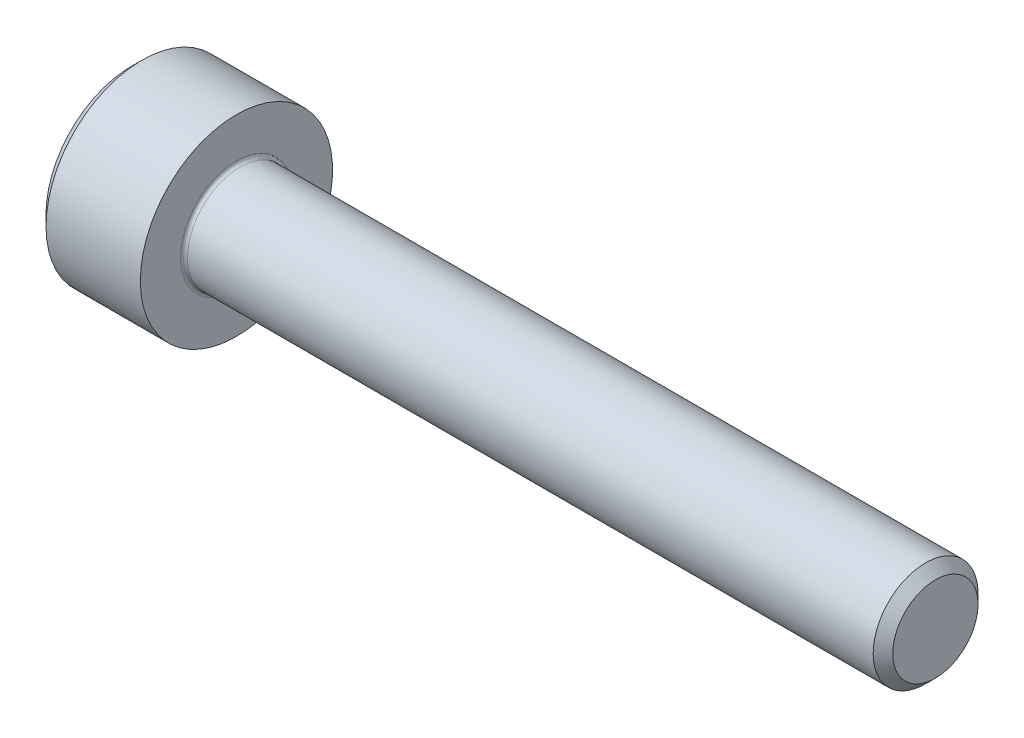
SolidWorks part; units mm, degrees
revolve "Base-Revolve" add sketch "BodySke"
sketch "BodySke" plane through (0, 0, 0) normal (0, 0, 1) x (1, 0, 0)
  line L0 (0, 0) -> (0, 2.45)
  line L1 (0.3, 2.75) -> (3, 2.75)
  line L2 (3, 2.75) -> (3, 1.5)
  line L3 (3, 1.5) -> (22.7195, 1.5)
  line L4 (23, 1.2195) -> (23, 0)
  line L5 (23, 0) -> (0, 0)
  line L6 (-31.75, 0) -> (127, 0) construction
  line L7 (0, 2.45) -> (0.3, 2.75)
  line L8 (23, 1.2195) -> (22.7195, 1.5)
  line L9 (0, -2.45) -> (0.3, -2.75) construction
  line L10 (23, -1.2195) -> (22.7195, -1.5) construction
  line L11 (3.5, 9.525) -> (3.5, 3.175) construction
  line L12 (3, 9.525) -> (3, 3.175) construction
  line L13 (-27, 9.525) -> (-27, 3.175) construction
  dimension "Diameter" = 3
  dimension "Head_ht" = 3
  dimension "Length" = 20
  dimension "Body_ch_ang" = 45
  dimension "Head_dia" = 5.5
  dimension "Head_ch_ang" = 45
  dimension "Minor_dia" = 2.439
  dimension "Advance" = 0.5
  dimension "Thread_nom" = 20
  dimension "Thread_length" = 50
  dimension "Head_ch_ht" = 0.3
cosmetic thread "ThreadCosmetic"
fillet "Fillet1" radius 0.1 1 edges at (3, 0, 1.5)
ref_plane "Plane1" through (0, 0, 0) normal (0, 0, 1) x (1, 0, 0)
ref_plane "Plane2" through (0, 0, 0) normal (0, 1, 0) x (1, 0, 0)
ref_plane "Plane3" through (0, 0, 0) normal (1, 0, 0) x (0, 0, -1)
sketch "Sketch2" plane through (0, 0, 0) normal (0, 0, 1) x (1, 0, 0)
  line L0 (0, 1.28) -> (1.3, 1.28)
  line L1 (1.3, 1.28) -> (2.039, 0)
  line L2 (-31.75, 0) -> (127, 0) construction
  line L3 (2.039, 0) -> (0, 0)
  line L4 (0, 0) -> (0, 1.28)
  line L5 (0, 2.45) -> (0, -2.45) construction
  line L6 (0, 0) -> (47.625, 0) construction
  line L7 (3, -2.75) -> (3, 2.75) construction
  dimension "D1" = 1.28
  dimension "D2" = 60
revolve "Hex-PreBroach" cut sketch "Sketch2" angle 360 about L6
sketch "Sketch3" plane through (0, 0, 0) normal (-1, 0, 0) x (0, 0.5, 0.866)
  line L0 (0.739, 1.28) -> (-0.739, 1.28)
  line L1 (-0.739, 1.28) -> (-1.478, 0)
  line L2 (0.739, 1.28) -> (1.478, 0)
  line L3 (0.739, -1.28) -> (1.478, 0)
  line L4 (0.739, -1.28) -> (-0.739, -1.28)
  line L5 (-0.739, -1.28) -> (-1.478, 0)
  dimension "D1" = 1.28
  dimension "D2" = 1.28
  dimension "Hex_size" = 2.56
extrude "Hex" cut sketch "Sketch3" against normal blind 1.3
sketch "Sketch4" plane through (0, 0, 0) normal (-1, 0, 0) x (0, 0, 1)
  line L0 (0, 0) -> (1.4605, 0)
  line L1 (0, 0) -> (6.1484, 3.5498) construction
  line L2 (0, 0) -> (0.7302, 1.2648)
  line L3 (1.2009, 0.3267) -> (1.3933, 0.4378)
  line L4 (0.8834, 0.8767) -> (1.0758, 0.9877)
  arc A0 (1.2009, 0.3267) -> (0.8834, 0.8767) centre (0, 0) ccw
  arc A1 (1.4605, 0) -> (1.3933, 0.4378) centre (0, 0) ccw
  arc A2 (0.7302, 1.2648) -> (1.0758, 0.9877) centre (0, 0) cw
  dimension "D1" = 30
  dimension "D2" = 60
  dimension "Spline_p_dim" = 0.635
  dimension "D3" = 0.3175
extrude "Spline" [suppressed] cut sketch "Sketch4" against normal blind 1.3
pattern_circular "CirPattern1" [suppressed] count 6 every 60
sketch "Sketch5" plane through (0, 0, 0) normal (0, 0, 1) x (1, 0, 0)
  line L0 (-31.75, 0) -> (127, 0) construction
  line L2 (0, 2.45) -> (0, -2.45) construction
  circle A0 centre (1.2, 0) radius 0.475
  dimension "Drilled_hole_dia" = 0.95
  dimension "Drilled_hole_loc" = 1.2
extrude "Hole" [suppressed] cut sketch "Sketch5" against normal through all and the other way through all
pattern_circular "Drilled-4" [suppressed] count 2 every 60
pattern_circular "Drilled-6" [suppressed] count 3 every 60
sketch "ThdSchSke" plane through (0, 0, 0) normal (0, 0, 1) x (1, 0, 0)
  line L0 (3.5, -1.2195) -> (3.3036, -1.5)
  line L1 (3.5, -1.2195) -> (3.6964, -1.5)
  line L2 (3.6964, -1.5) -> (3.6964, -1.875)
  line L3 (-3.175, 0) -> (5.1513, 0) construction
  line L5 (3.6964, -1.875) -> (3.3036, -1.875)
  line L6 (3.3036, -1.875) -> (3.3036, -1.5)
  line L7 (0, 2.45) -> (0, -2.45) construction
  dimension "Thread_minor" = 2.439
  dimension "Diameter" = 3
  dimension "Start" = 3.5
revolve "ThreadSchematic" [suppressed] cut sketch "ThdSchSke" angle 360 about L3
pattern_linear "ThdSchPat" [suppressed]
sketch "Sketch6" plane through (0, 0, 0) normal (-1, 0, 0) x (0, 0, 1)
  circle A0 centre (0, 0) radius 2.75 construction
  circle A1 centre (0, 0) radius 2.75
extrude "Cut-Extrude1" [suppressed] cut sketch "Sketch6" against normal offset from surface (2 mm away) 1
equation "\"D2@Sketch3\" = \"Hex_size@Sketch3\" / 2"
equation "\"D1@Sketch3\" = \"Hex_size@Sketch3\" / 2"
equation "\"D1@Sketch2\" = \"Hex_size@Sketch3\" / 2"
equation "\"D3@Sketch4\" = \"Spline_p_dim@Sketch4\" / 2"
equation "\"Thread_minor@ThreadCosmetic\"  =  \"Minor_dia@BodySke\""
equation "\"D2@CirPattern1\" = 360 / \"Num_teeth@CirPattern1\""
equation "\"Wall_thickness@Sketch2\" = \"Head_ht@BodySke\" - \"Key_eng@Hex\""
equation "\"Thread_length@ThreadCosmetic\" = ((sgn( (\"Length@BodySke\" - \"Advance@BodySke\" ) - \"Thread_nom@BodySke\" )-1)*( (\"Length@BodySke\" - \"Advance@BodySke\" ) - \"Thread_nom@BodySke\" ))/-2+ \"Thread_nom@BodySke\""
equation "\"Thread_minor@ThdSchSke\" = \"Minor_dia@BodySke\""
equation "\"Diameter@ThdSchSke\" = \"Diameter@BodySke\""
equation "\"Overcut@ThdSchSke\" = \"Diameter@BodySke\" * 1.25"
equation "\"Start@ThdSchSke\" = \"Head_ht@BodySke\" + \"Length@BodySke\" - \"Thread_length@ThreadCosmetic\"  '---Non-countersunk---"
equation "\"Num_threads@ThdSchPat\" = int( \"Thread_length@ThreadCosmetic\" / \"Advance@BodySke\" + 0.999 )  + 1"
equation "\"Advance@ThdSchPat\" = \"Thread_length@ThreadCosmetic\" /  (\"Num_threads@ThdSchPat\" - 1) 'relax it"
equation "\"Num_threads@ThdSchPat\" = \"Num_threads@ThdSchPat\" - sgn( \"Num_threads@ThdSchPat\" - 1) '---chamfered tips only---"
